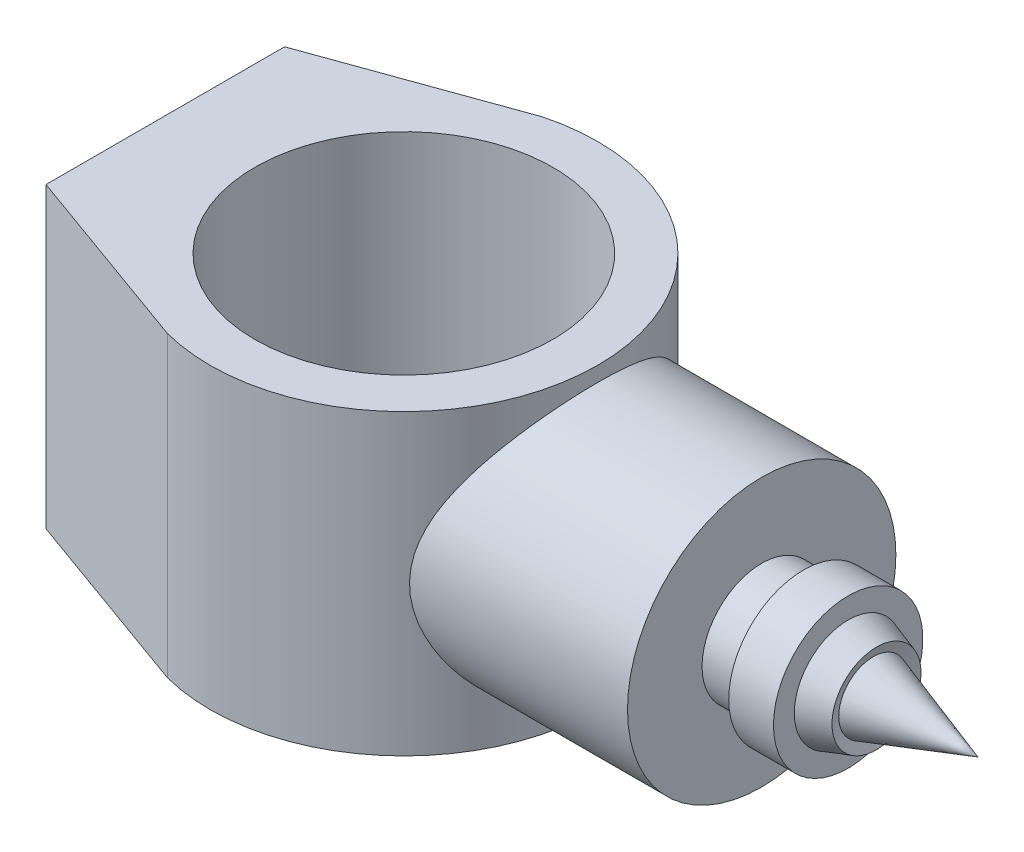
SolidWorks part; units mm, degrees
ref_plane "Front Plane" through (0, 0, 0) normal (0, 0, 1) x (1, 0, 0)
ref_plane "Top Plane" through (0, 0, 0) normal (0, 1, 0) x (1, 0, 0)
ref_plane "Right Plane" through (0, 0, 0) normal (1, 0, 0) x (0, 0, -1)
sketch "Sketch1" plane through (0, 0, 0) normal (0, 1, 0) x (1, 0, 0)
  line L0 (-80, -40) -> (-80, 40)
  line L1 (-80, 40) -> (-16.4074, 62.8951)
  line L2 (-80, -40) -> (-16.4074, -62.8951)
  arc A0 (-16.4074, -62.8951) -> (-16.4074, 62.8951) centre (0, 0) ccw
  circle A1 centre (0, 0) radius 50
  point P7 (-80, 0)
  dimension "D1" = 130
  dimension "D2" = 100
  dimension "D3" = 80
  dimension "D4" = 80
extrude "Boss-Extrude1" add sketch "Sketch1" along normal mid plane 100
ref_plane "Plane1" through (120, 0, 0) normal (1, 0, 0) x (0, 0, -1)
sketch "Sketch2" plane through (120, 0, 0) normal (1, 0, 0) x (0, 0, -1)
  circle A0 centre (0, 0) radius 45
  dimension "D1" = 90
extrude "Boss-Extrude2" add sketch "Sketch2" against normal up to next
sketch "Sketch3" plane through (0, 0, 0) normal (0, 1, 0) x (1, 0, 0)
  line L0 (0, 0) -> (252.5523, 0) construction
  line L1 (120, 0) -> (120, -20)
  line L2 (120, -45) -> (120, 45) construction
  line L3 (120, -20) -> (134, -20)
  line L4 (134, -20) -> (134, -25.0513)
  line L5 (134, -25.0513) -> (149, -25.0513)
  line L6 (149, -25.0513) -> (149, -18.0513)
  line L7 (149, -18.0513) -> (158.4993, -14.9268)
  line L8 (158.4993, -14.9268) -> (157.3922, -11.5606)
  line L9 (157.3922, -11.5606) -> (192.5397, 0)
  line L10 (192.5397, 0) -> (120, 0)
  dimension "D1" = 20
  dimension "D2" = 14
  dimension "D3" = 15
  dimension "D4" = 10
  dimension "D5" = 37
  dimension "D7" = 7
  dimension "D8" = 18.207
revolve "Revolve1" add sketch "Sketch3" angle 360 about L0
